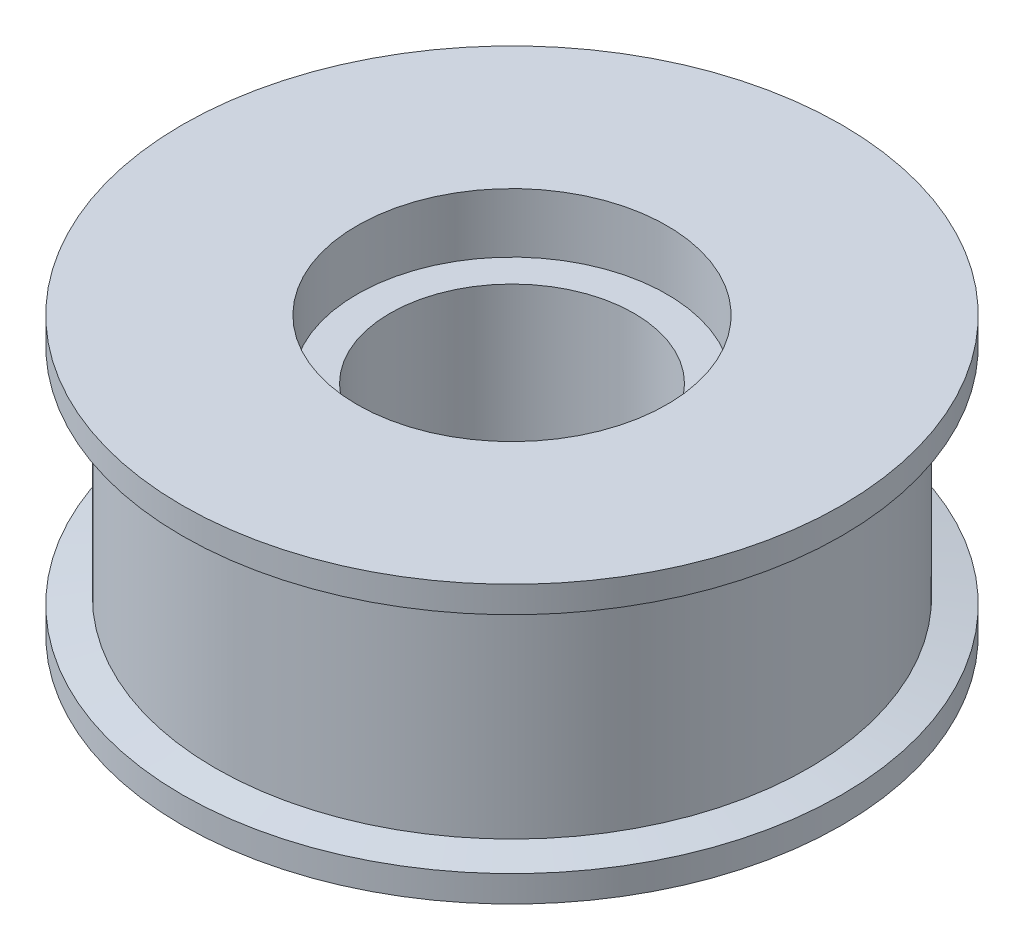
SolidWorks part; units mm, degrees
material "AISI 1045 钢，冷拔"
ref_plane "前视基准面" through (0, 0, 0) normal (0, 0, 1) x (1, 0, 0)
ref_plane "上视基准面" through (0, 0, 0) normal (0, 1, 0) x (1, 0, 0)
ref_plane "右视基准面" through (0, 0, 0) normal (1, 0, 0) x (0, 0, -1)
sketch "草图1" plane through (0, 0, 0) normal (0, 0, 1) x (1, 0, 0)
  line L0 (0, 49.7269) -> (0, -62.6139) construction
  line L1 (-23.5, -14) -> (-23.5, -23)
  line L2 (-23.5, 19) -> (-23.5, 10)
  line L3 (-45, 14) -> (-45, -18)
  line L4 (-50, 19) -> (-50, 15)
  line L5 (0, 0) -> (-105.5745, 0) construction
  line L6 (-23.5, 19) -> (-50, 19)
  line L7 (-23.5, -23) -> (-50, -23)
  line L8 (-50, -19) -> (-50, -23)
  line L9 (0, 19) -> (-105.5745, 19) construction
  line L10 (0, -23) -> (-105.5745, -23) construction
  line L11 (-50, 49.7269) -> (-50, -62.6139) construction
  line L12 (-45, 49.7269) -> (-45, -62.6139) construction
  line L13 (-23.5, 49.7269) -> (-23.5, -62.6139) construction
  line L14 (0, 10) -> (-50, 10) construction
  line L15 (-18.5, 10) -> (-23.5, 10)
  line L16 (-18.5, -14) -> (-23.5, -14)
  line L17 (-18.5, 10) -> (-18.5, -14)
  line L18 (0, -14) -> (-50, -14) construction
  line L19 (-18.5, 19) -> (-18.5, -23) construction
  line L20 (-50, 15) -> (-45, 14)
  line L21 (-45, -18) -> (-50, -19)
  line L23 (-23.5, 19) -> (-23.5, -23) construction
  line L24 (0, 19) -> (-50, 19) construction
  line L25 (0, -23) -> (-50, -23) construction
  point P3 (-12.5, 49.7269)
  point P4 (-12.5, -62.6139)
  dimension "D5" = 4
  dimension "D9" = 1
  dimension "D10" = 5
  dimension "D6" = 4
  dimension "D11" = 1
  dimension "D12" = 42
  dimension "D2" = 23.5
  dimension "D3" = 45
  dimension "D4" = 50
  dimension "D7" = 9
  dimension "D8" = 9
revolve "旋转1" add sketch "草图1" angle 360 about L0
